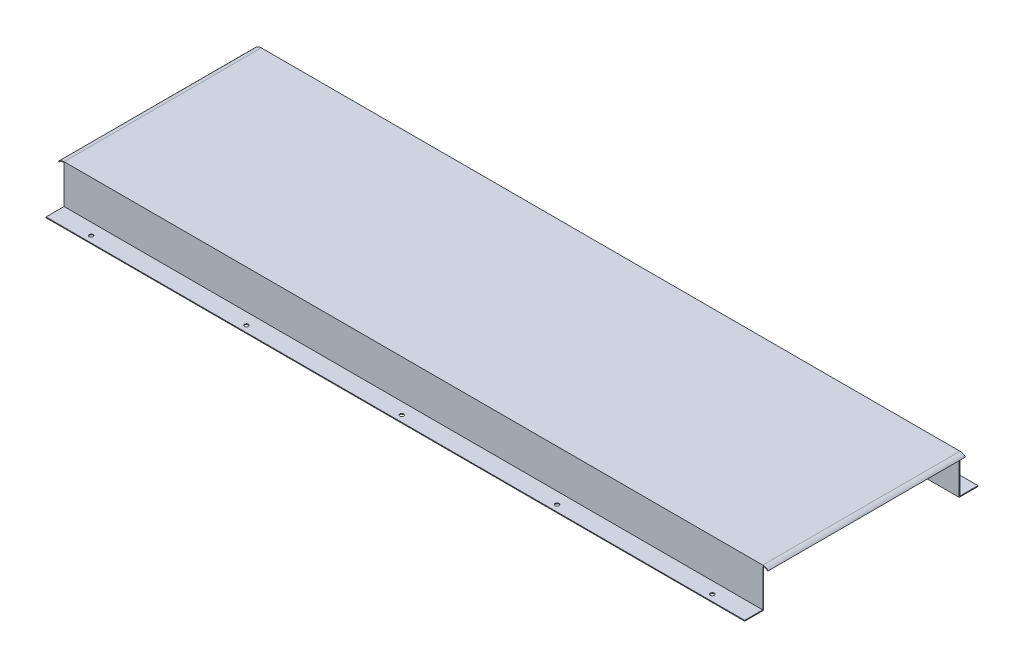
SolidWorks part; units mm, degrees
ref_plane "Front Plane" through (0, 0, 0) normal (0, 0, 1) x (1, 0, 0)
ref_plane "Top Plane" through (0, 0, 0) normal (0, 1, 0) x (1, 0, 0)
ref_plane "Right Plane" through (0, 0, 0) normal (1, 0, 0) x (0, 0, -1)
sketch "Sketch2" plane through (0, 0, 0) normal (0, 0, 1) x (1, 0, 0)
  line L1 (450, 25.5) -> (-450, 25.5)
  line L2 (450, 25.5) -> (450, -25.5)
  line L3 (450, -25.5) -> (-450, -25.5)
  line L4 (-450, 25.5) -> (-450, -25.5)
  line L5 (450, 25.5) -> (-450, -25.5) construction
  line L6 (450, -25.5) -> (-450, 25.5) construction
  point P0 (0, 0)
  dimension "D1" = 51
  dimension "D2" = 900
extrude "Boss-Extrude1" add sketch "Sketch2" along normal blind 1
sketch "Sketch3" plane through (0, 0, 0) normal (0, 0, 1) x (1, 0, 0)
  line L0 (-450, -24.5) -> (450, -24.5)
  line L1 (-450, 25.5) -> (-450, -25.5) construction
  line L2 (450, -25.5) -> (450, 25.5) construction
  line L3 (450, -24.5) -> (450, -25.5)
  line L4 (450, -25.5) -> (-450, -25.5)
  line L5 (-450, -25.5) -> (-450, -24.5)
  dimension "D1" = 1
extrude "Boss-Extrude2" add sketch "Sketch3" against normal blind 23.25
ref_plane "Plane1" through (0, 0, 127) normal (0, 0, 1) x (1, 0, 0)
sketch "Sketch4" plane through (0, 0, 0) normal (0, 0, 1) x (1, 0, 0)
  line L0 (450, 25.5) -> (-450, 25.5)
  line L1 (-450, 25.5) -> (-450, 24.5)
  line L2 (-450, 25.5) -> (-450, -24.5) construction
  line L3 (-450, 24.5) -> (450, 24.5)
  line L4 (450, -24.5) -> (450, 25.5) construction
  line L5 (450, 24.5) -> (450, 25.5)
  dimension "D1" = 1
extrude "Boss-Extrude3" add sketch "Sketch4" along normal blind 126 from offset 1
sketch "Sketch5" plane through (0, 0, 0) normal (0, 1, 0) x (1, 0, 0)
  line L3 (450, 23.25) -> (450, 0) construction
  line L6 (-450, -1) -> (450, -1) construction
  circle A0 centre (400, 15) radius 2.5
  point P8 (399.8494, 14.8664)
  dimension "D1" = 5
  dimension "D2" = 16
  dimension "D3" = 50
extrude "Cut-Extrude1" cut sketch "Sketch5" against normal through all both and the other way through all
pattern_linear "LPattern2" count 6 spacing 200 along (-1, 0, 0) of "Cut-Extrude1"
sketch "Sketch7" plane through (0, 0, 0) normal (0, 0, 1) x (1, 0, 0)
  line L5 (-450, 25.5) -> (-450, -24.5) construction
  line L16 (-450, 24.5) -> (-450, 25.5)
  line L18 (-456.364, 21.864) -> (-457.0711, 22.5711)
  arc A11 (-450, 25.5) -> (-457.0711, 22.5711) centre (-450, 15.5) ccw
  arc A12 (-450, 24.5) -> (-456.364, 21.864) centre (-450, 15.5) ccw
  point P4 (420, 15.5)
  point P5 (420, 15.5)
  point P14 (-420, 15.5)
  point P22 (-420, 15.5)
  dimension "D1" = 45
extrude "Boss-Extrude4" add sketch "Sketch7" along normal blind 127
sketch "Sketch8" plane through (0, 0, 0) normal (0, 0, 1) x (1, 0, 0)
  line L0 (450, -24.5) -> (450, 25.5) construction
  line L1 (456.364, 21.864) -> (457.0711, 22.5711)
  line L2 (450, 25.5) -> (450, 24.5)
  arc A0 (450, 25.5) -> (457.0711, 22.5711) centre (450, 15.5) cw
  arc A1 (450, 24.5) -> (456.364, 21.864) centre (450, 15.5) cw
  dimension "D1" = 45
  dimension "D2" = 1
extrude "Boss-Extrude5" add sketch "Sketch8" along normal blind 127
mirror "Mirror2" about plane through (0, 0, 127) normal (0, 0, 1) of "Boss-Extrude4", "Boss-Extrude5", "Boss-Extrude3"
mirror "Mirror4" about plane through (0, 0, 127) normal (0, 0, 1) of "LPattern2", "Cut-Extrude1", "Boss-Extrude2", "Boss-Extrude1"
